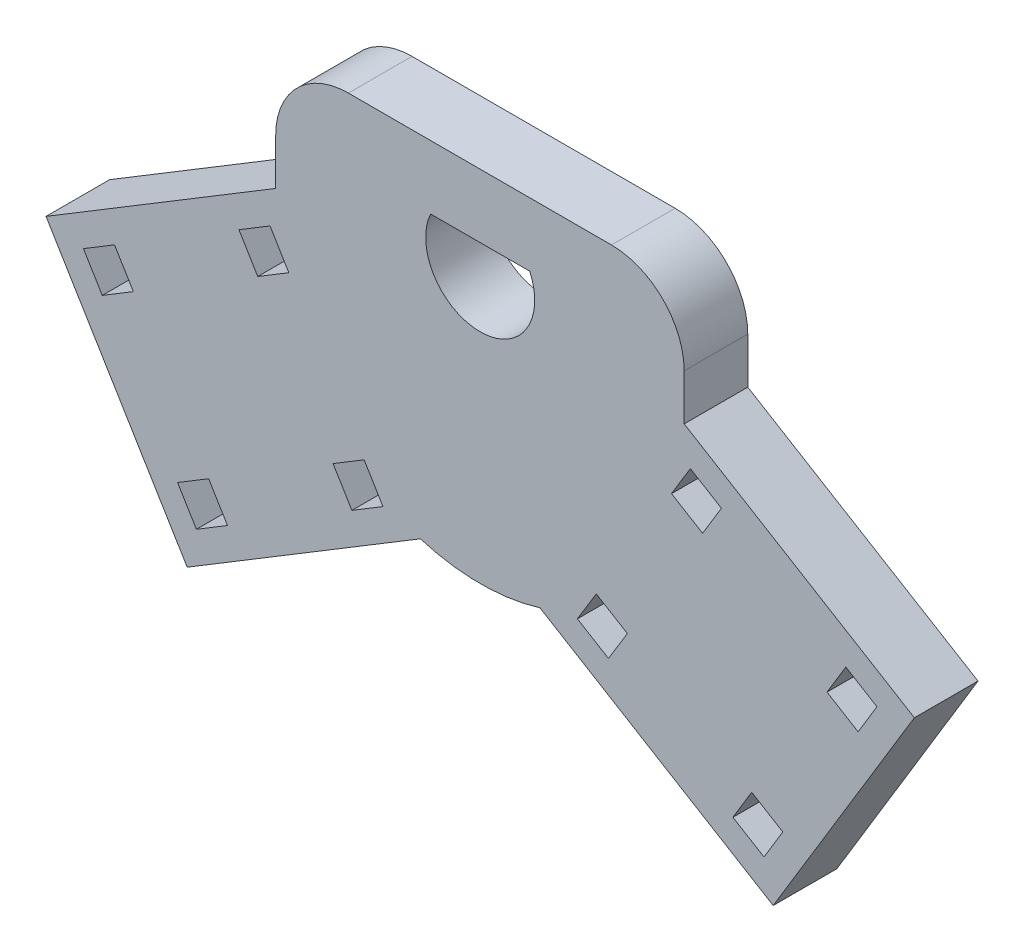
SolidWorks part; units mm, degrees
material "PLA 15%"
ref_plane "Front Plane" through (0, 0, 0) normal (0, 0, 1) x (1, 0, 0)
ref_plane "Top Plane" through (0, 0, 0) normal (0, 1, 0) x (1, 0, 0)
ref_plane "Right Plane" through (0, 0, 0) normal (1, 0, 0) x (0, 0, -1)
sketch "Sketch2" plane through (0, 0, 0) normal (0, 0, 1) x (1, 0, 0)
  line L8 (0, 0) -> (0, -22.5) construction
  line L9 (0, 0) -> (6.5784, -21.5169)
  line L10 (0, 0) -> (-6.5784, -21.5169)
  line L11 (6.5784, -21.5169) -> (22.1146, 4.1469)
  line L12 (6.5784, -21.5169) -> (32.2421, -37.053)
  line L13 (22.1146, 4.1469) -> (47.7783, -11.3893)
  line L14 (32.2421, -37.053) -> (47.7783, -11.3893)
  line L15 (-6.5784, -21.5169) -> (-22.1146, 4.1469)
  line L16 (-6.5784, -21.5169) -> (-32.2421, -37.053)
  line L17 (-22.1146, 4.1469) -> (-47.7783, -11.3893)
  line L18 (-32.2421, -37.053) -> (-47.7783, -11.3893)
  line L24 (22.1146, 17.2594) -> (22.1146, 4.1469)
  line L30 (0, 0) -> (0, 15)
  line L31 (-22.5, 15) -> (-22.5, 0)
  line L32 (-22.5, 15) -> (22.4447, 15)
  line L33 (-22.5, 0) -> (22.4447, 0)
  line L34 (22.4447, 15) -> (22.4447, 0)
  circle A0 centre (0, 0) radius 22.5
  circle A2 centre (0, 15) radius 22.5
  dimension "D5" = 45
  dimension "D8" = 15
  dimension "D9" = 45
  dimension "D1" = 17
  dimension "D2" = 17
  dimension "D3" = 30
  dimension "D4" = 30
  dimension "D6" = 30
  dimension "D7" = 30
extrude "Boss-Extrude1" add sketch "Sketch2" along normal blind 7
sketch "Sketch4" plane through (0, 0, 7) normal (0, 0, 1) x (1, 0, 0)
  line L0 (-22.1146, 4.1469) -> (-6.5784, -21.5169)
  line L1 (-22.5, 3.9135) -> (-47.7783, -11.3893) construction
  line L2 (-6.5784, -21.5169) -> (-32.2421, -37.053) construction
  line L3 (-32.2421, -37.053) -> (-47.7783, -11.3893) construction
  line L4 (6.5784, -21.5169) -> (22.1146, 4.1469)
  line L5 (-46.2247, -13.9557) -> (-20.5609, 1.5805)
  line L6 (-22.5, 3.9135) -> (-47.7783, -11.3893) construction
  line L7 (6.5784, -21.5169) -> (32.2421, -37.053) construction
  line L8 (22.4447, 3.947) -> (47.7783, -11.3893) construction
  line L9 (32.2421, -37.053) -> (47.7783, -11.3893) construction
  line L10 (-43.6583, -12.4021) -> (-29.6757, -35.4994)
  line L11 (-31.2293, -32.9331) -> (-8.132, -18.9505)
  line L12 (-23.1273, 0.0269) -> (-10.6984, -20.5041)
  line L13 (-43.6583, -12.4021) -> (-40.2365, -10.3306)
  line L14 (-43.6583, -12.4021) -> (-41.5868, -15.8239)
  line L15 (-40.2365, -10.3306) -> (-38.165, -13.7524)
  line L16 (-41.5868, -15.8239) -> (-38.165, -13.7524)
  line L17 (-23.1273, 0.0269) -> (-26.5491, -2.0446)
  line L18 (-23.1273, 0.0269) -> (-21.0558, -3.395)
  line L19 (-26.5491, -2.0446) -> (-24.4776, -5.4664)
  line L20 (-21.0558, -3.395) -> (-24.4776, -5.4664)
  line L21 (-31.2293, -32.9331) -> (-33.3008, -29.5112)
  line L22 (-31.2293, -32.9331) -> (-27.8075, -30.8616)
  line L23 (-33.3008, -29.5112) -> (-29.879, -27.4397)
  line L24 (-27.8075, -30.8616) -> (-29.879, -27.4397)
  line L25 (-10.6984, -20.5041) -> (-12.7698, -17.0823)
  line L26 (-10.6984, -20.5041) -> (-14.1202, -22.5756)
  line L27 (-12.7698, -17.0823) -> (-16.1917, -19.1538)
  line L28 (-14.1202, -22.5756) -> (-16.1917, -19.1538)
  line L29 (20.5609, 1.5805) -> (46.2247, -13.9557)
  line L30 (22.4447, 3.947) -> (47.7783, -11.3893) construction
  line L31 (43.6583, -12.4021) -> (29.6757, -35.4994)
  line L32 (31.2293, -32.9331) -> (8.132, -18.9505)
  line L33 (10.6984, -20.5041) -> (23.1273, 0.0269)
  line L34 (23.1273, 0.0269) -> (26.5491, -2.0446)
  line L35 (23.1273, 0.0269) -> (21.0558, -3.395)
  line L36 (26.5491, -2.0446) -> (24.4776, -5.4664)
  line L37 (21.0558, -3.395) -> (24.4776, -5.4664)
  line L38 (43.6583, -12.4021) -> (40.2365, -10.3306)
  line L39 (43.6583, -12.4021) -> (41.5868, -15.8239)
  line L40 (40.2365, -10.3306) -> (38.165, -13.7524)
  line L41 (41.5868, -15.8239) -> (38.165, -13.7524)
  line L42 (31.2293, -32.9331) -> (33.3008, -29.5112)
  line L43 (31.2293, -32.9331) -> (27.8075, -30.8616)
  line L44 (33.3008, -29.5112) -> (29.879, -27.4397)
  line L45 (27.8075, -30.8616) -> (29.879, -27.4397)
  line L46 (10.6984, -20.5041) -> (12.7698, -17.0823)
  line L47 (10.6984, -20.5041) -> (14.1202, -22.5756)
  line L48 (12.7698, -17.0823) -> (16.1917, -19.1538)
  line L49 (14.1202, -22.5756) -> (16.1917, -19.1538)
  circle A0 centre (-40.9116, -13.0772) radius 2
  circle A1 centre (-23.8025, -2.7198) radius 2
  circle A2 centre (-13.445, -19.8289) radius 2
  circle A3 centre (-30.5542, -30.1864) radius 2
  circle A4 centre (23.8025, -2.7198) radius 2
  circle A6 centre (13.445, -19.8289) radius 2
  circle A7 centre (40.9116, -13.0772) radius 2
  circle A8 centre (30.5542, -30.1864) radius 2
  dimension "D10" = 4
  dimension "D11" = 4
  dimension "D12" = 4
  dimension "D13" = 4
  dimension "D19" = 4
  dimension "D20" = 4
  dimension "D25" = 4
  dimension "D26" = 4
  dimension "D1" = 30
  dimension "D2" = 5
  dimension "D3" = 5
  dimension "D4" = 5
  dimension "D5" = 5
  dimension "D6" = 5
  dimension "D7" = 5
  dimension "D8" = 5
  dimension "D9" = 5
  dimension "D14" = 30
  dimension "D15" = 5
  dimension "D16" = 5
  dimension "D17" = 5
  dimension "D18" = 5
  dimension "D21" = 5
  dimension "D22" = 5
  dimension "D23" = 5
  dimension "D24" = 5
  dimension "D27" = 3
  dimension "D28" = 3
  dimension "D29" = 3
  dimension "D30" = 3
  dimension "D31" = 4
  dimension "D32" = 4
  dimension "D33" = 4
  dimension "D34" = 4
  dimension "D35" = 4
  dimension "D36" = 4
  dimension "D37" = 4
  dimension "D38" = 4
  dimension "D39" = 3
  dimension "D40" = 3
  dimension "D41" = 3
  dimension "D42" = 3
  dimension "D43" = 4
  dimension "D44" = 4
  dimension "D45" = 4
  dimension "D46" = 4
  dimension "D47" = 4
  dimension "D48" = 4
  dimension "D49" = 4
  dimension "D50" = 4
extrude "Cut-Extrude1" cut sketch "Sketch4" against normal blind 10 contours A0 | A1 | A2 | A3 | A6 | A4 | A7 | A8 | L17 L18 L20 L19 | L25 L26 L28 L27 | L21 L22 L24 L23 | L13 L14 L16 L15 | L46 L47 L49 L48 | L34 L35 L37 L36 | L38 L39 L41 L40 | L42 L43 L45 L44
sketch "Sketch5" plane through (0, 0, 7) normal (0, 0, 1) x (1, 0, 0)
  line L0 (0, 22.5) -> (0, -22.5)
  line L2 (5.4544, 10) -> (-5.4544, 10)
  arc A0 (-6.5784, -21.5169) -> (6.5784, -21.5169) centre (0, 0) ccw construction
  arc A1 (-6.5784, -21.5169) -> (6.5784, -21.5169) centre (0, 0) ccw construction
  arc A2 (-5.4544, 10) -> (5.4544, 10) centre (0, 7.5) ccw
  dimension "D2" = 12
  dimension "D1" = 30
  dimension "D3" = 2.5
extrude "Cut-Extrude2" cut sketch "Sketch5" against normal blind 10 contours A2 L2
sketch "Sketch6" plane through (0, 0, 0) normal (0, 0, 1) x (1, 0, 0)
  line L0 (5.4544, 10) -> (-5.4544, 10) construction
  line L1 (-34.6956, 17) -> (33.2006, 17)
  line L2 (-34.6956, 17) -> (-34.6956, 43.411)
  line L3 (-34.6956, 43.411) -> (33.2006, 43.411)
  line L4 (33.2006, 17) -> (33.2006, 43.411)
  point P6 (0, 10)
  dimension "D1" = 7
extrude "Cut-Extrude3" cut sketch "Sketch6" along normal through all both and the other way through all
fillet "Fillet1" radius 8 2 edges at (22.4109, 17, 3.5) (-22.4109, 17, 3.5)
